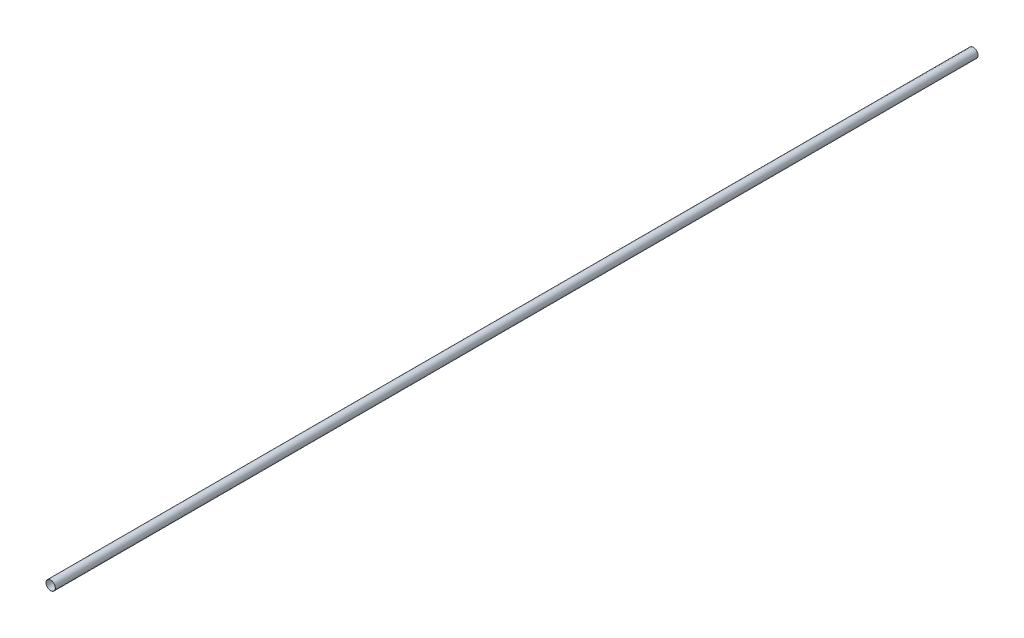
SolidWorks part; units mm, degrees
material "Gray Cast Iron"
ref_plane "Front Plane" through (0, 0, 0) normal (0, 0, 1) x (1, 0, 0)
ref_plane "Top Plane" through (0, 0, 0) normal (0, 1, 0) x (1, 0, 0)
ref_plane "Right Plane" through (0, 0, 0) normal (1, 0, 0) x (0, 0, -1)
sketch "Sketch1" plane through (0, 0, 0) normal (0, 0, 1) x (1, 0, 0)
  circle A0 centre (0, 0) radius 101
  circle A1 centre (0, 0) radius 100
extrude "Boss-Extrude1" add sketch "Sketch1" along normal blind 20000
